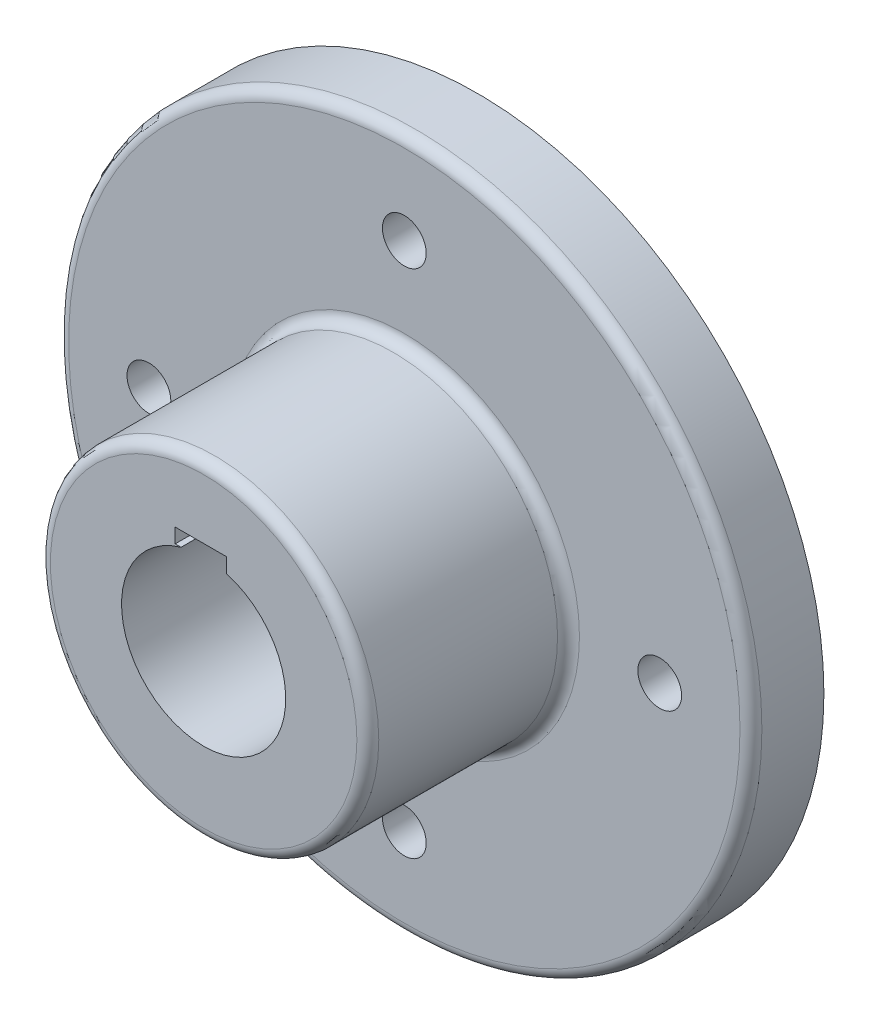
SolidWorks part; units mm, degrees
ref_plane "Front Plane" through (0, 0, 0) normal (0, 0, 1) x (1, 0, 0)
ref_plane "Top Plane" through (0, 0, 0) normal (0, 1, 0) x (1, 0, 0)
ref_plane "Right Plane" through (0, 0, 0) normal (1, 0, 0) x (0, 0, -1)
sketch "Sketch2" plane through (0, 0, 0) normal (0, 0, 1) x (1, 0, 0)
  circle A0 centre (0, 0) radius 95
  dimension "D1" = 190
extrude "Boss-Extrude1" add sketch "Sketch2" along normal blind 20
sketch "Sketch3" plane through (0, 0, 20) normal (0, 0, 1) x (1, 0, 0)
  circle A0 centre (0, 0) radius 45
  dimension "D1" = 90
extrude "Boss-Extrude2" add sketch "Sketch3" along normal blind 55
sketch "Sketch4" plane through (0, 0, 0) normal (0, 0, -1) x (-1, 0, 0)
  circle A0 centre (0, 0) radius 22.5
  dimension "D1" = 45
extrude "Cut-Extrude1" cut sketch "Sketch4" against normal up to surface (75 mm away) up to face at (45, 0, 75)
sketch "Sketch5" plane through (0, 0, 0) normal (0, 0, -1) x (-1, 0, 0)
  circle A0 centre (0, 70) radius 6
  circle A1 centre (70, 0) radius 6
  circle A2 centre (0, -70) radius 6
  circle A3 centre (-70, 0) radius 6
  point P12 (0, 0)
  dimension "D1" = 12
  dimension "D2" = 70
  dimension "D3" = 4
extrude "Cut-Extrude2" cut sketch "Sketch5" against normal up to surface (20 mm away) up to face at (45, 0, 20)
sketch "Sketch6" plane through (0, 0, 0) normal (0, 0, -1) x (-1, 0, 0)
  line L1 (-6.1983, 21.6294) -> (7.8017, 21.6294)
  line L2 (-6.1983, 21.6294) -> (-6.1983, 25.6294)
  line L3 (-6.1983, 25.6294) -> (7.8017, 25.6294)
  line L4 (7.8017, 21.6294) -> (7.8017, 25.6294)
  circle A1 centre (0, 0) radius 22.5 construction
  point P4 (0, 0)
  dimension "D1" = 4
  dimension "D2" = 14
extrude "Cut-Extrude3" cut sketch "Sketch6" against normal up to surface (75 mm away) up to face at (22.5, 0, 75)
fillet "Fillet1" radius 3 3 edges at (45, 0, 75) (45, 0, 20) (95, 0, 20)
